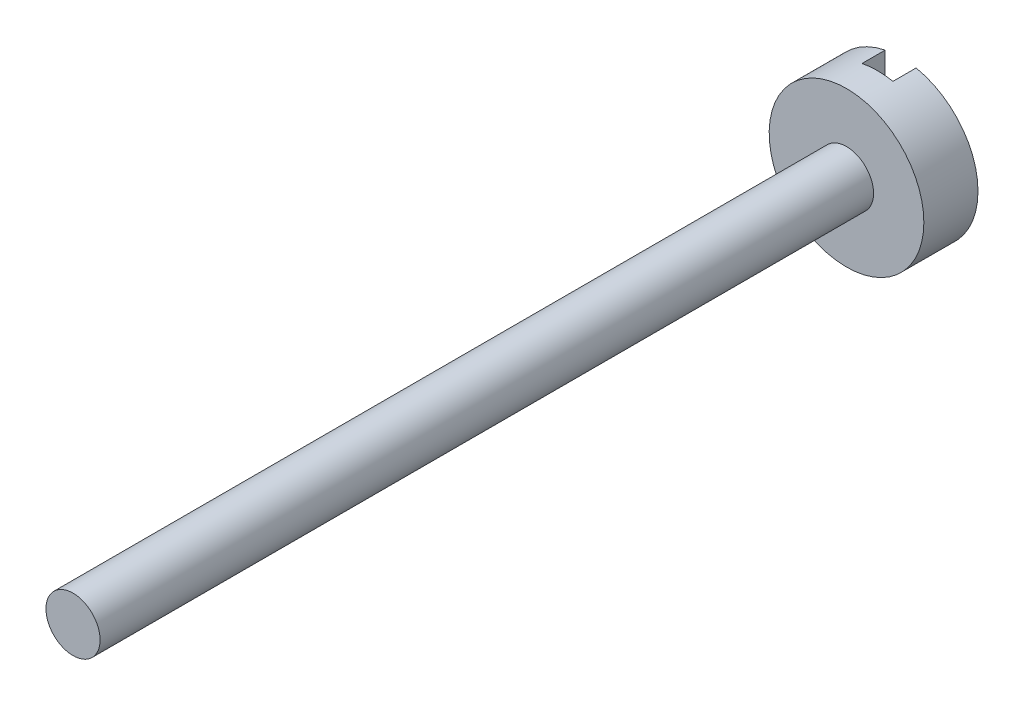
SolidWorks part; units mm, degrees
material "Plain Carbon Steel"
ref_plane "Front Plane" through (0, 0, 0) normal (0, 0, 1) x (1, 0, 0)
ref_plane "Top Plane" through (0, 0, 0) normal (0, 1, 0) x (1, 0, 0)
ref_plane "Right Plane" through (0, 0, 0) normal (1, 0, 0) x (0, 0, -1)
sketch "Sketch1" plane through (0, 0, 0) normal (0, 0, 1) x (1, 0, 0)
  circle A0 centre (0, 0) radius 1
  dimension "D1" = 2
extrude "Boss-Extrude1" add sketch "Sketch1" along normal blind 0.7
sketch "Sketch3" plane through (0, 0, 0.7) normal (0, 0, 1) x (1, 0, 0)
  circle A0 centre (0, 0) radius 0.35
  dimension "D1" = 0.7
extrude "Boss-Extrude2" add sketch "Sketch3" along normal blind 10
sketch "Sketch5" plane through (0, 0, 0) normal (0, 0, -1) x (-1, 0, 0)
  line L1 (-0.2, 1) -> (0.2, 1)
  line L2 (-0.2, 1) -> (-0.2, -1)
  line L3 (-0.2, -1) -> (0.2, -1)
  line L4 (0.2, 1) -> (0.2, -1)
  line L5 (-0.2, 1) -> (0.2, -1) construction
  line L6 (-0.2, -1) -> (0.2, 1) construction
  point P0 (0, 0)
  dimension "D1" = 0.4
  dimension "D2" = 2
extrude "Cut-Extrude1" cut sketch "Sketch5" against normal blind 0.3
